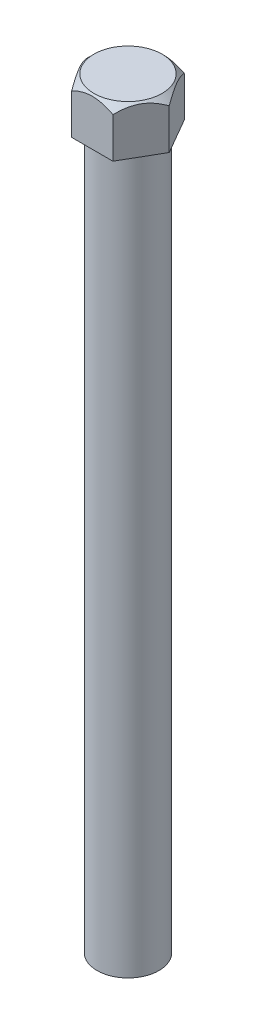
SolidWorks part; units mm, degrees
ref_plane "Front Plane" through (0, 0, 0) normal (0, 0, 1) x (1, 0, 0)
ref_plane "Top Plane" through (0, 0, 0) normal (0, 1, 0) x (1, 0, 0)
ref_plane "Right Plane" through (0, 0, 0) normal (1, 0, 0) x (0, 0, -1)
sketch "Sketch1" plane through (0, 0, 0) normal (0, 1, 0) x (1, 0, 0)
  circle A0 centre (0, 0) radius 0.13
  dimension "D1" = 0.26
extrude "Boss-Extrude1" add sketch "Sketch1" along normal blind 3.2
sketch "Sketch2" plane through (0, 3.2, 0) normal (0, 1, 0) x (1, 0, 0)
  line L1 (0.1732, 0) -> (0.0866, 0.15)
  line L2 (0.0866, 0.15) -> (-0.0866, 0.15)
  line L3 (-0.0866, 0.15) -> (-0.1732, 0)
  line L4 (-0.1732, 0) -> (-0.0866, -0.15)
  line L5 (-0.0866, -0.15) -> (0.0866, -0.15)
  line L6 (0.0866, -0.15) -> (0.1732, 0)
  circle A0 centre (0, 0) radius 0.15 construction
  dimension "D1" = 0.3
extrude "Boss-Extrude2" add sketch "Sketch2" against normal blind 0.2
sketch "Sketch3" plane through (0, 0, 0) normal (0, 0, 1) x (1, 0, 0)
  line L0 (0.1732, 3) -> (0.1732, 3.2) construction
  line L1 (0.0866, 3.2) -> (0.1732, 3.2) construction
  line L2 (0.1732, 3.2) -> (0.1732, 3.17)
  line L3 (0.1732, 3.2) -> (0.1432, 3.2)
  line L4 (0.1432, 3.2) -> (0.1732, 3.17)
  line L5 (0, 0) -> (0, 5.2135) construction
revolve "Cut-Revolve1" cut sketch "Sketch3" angle 360 about L5
